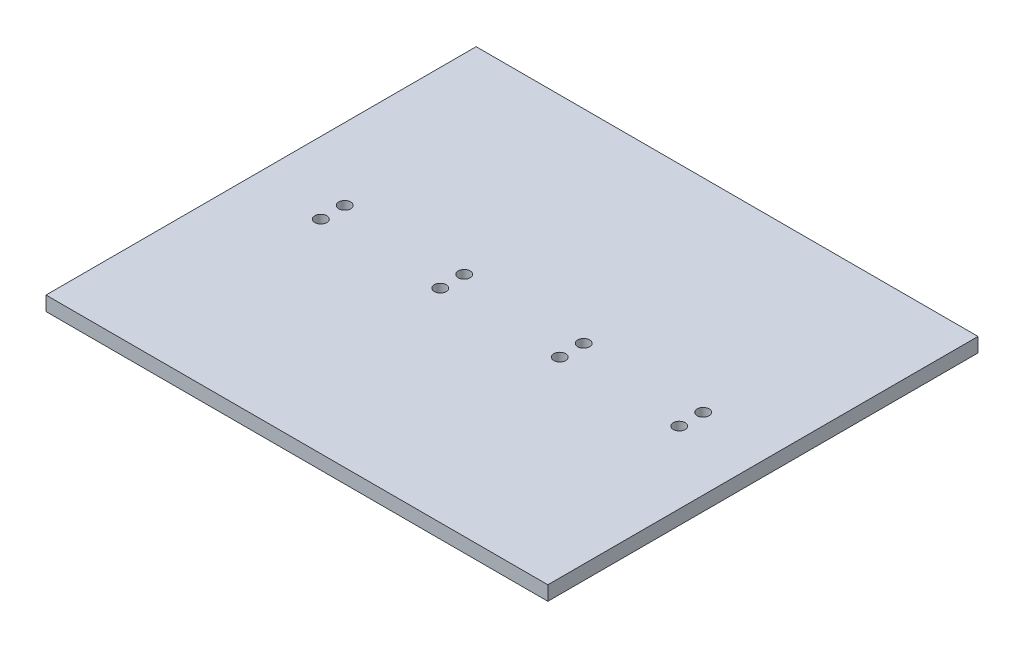
SolidWorks part; units mm, degrees
material "A-Стеклянное волокно"
ref_plane "Спереди" through (0, 0, 0) normal (0, 0, 1) x (1, 0, 0)
ref_plane "Сверху" through (0, 0, 0) normal (0, 1, 0) x (1, 0, 0)
ref_plane "Справа" through (0, 0, 0) normal (1, 0, 0) x (0, 0, -1)
sketch "Эскиз1" plane through (0, 0, 0) normal (0, 1, 0) x (1, 0, 0)
  line L1 (-5.25, -4.5) -> (5.25, -4.5)
  line L2 (-5.25, -4.5) -> (-5.25, 4.5)
  line L3 (-5.25, 4.5) -> (5.25, 4.5)
  line L4 (5.25, -4.5) -> (5.25, 4.5)
  line L5 (-5.25, -4.5) -> (5.25, 4.5) construction
  line L6 (-5.25, 4.5) -> (5.25, -4.5) construction
  point P0 (0, 0)
  dimension "D1" = 10.5
  dimension "D2" = 9
extrude "Бобышка-Вытянуть1" add sketch "Эскиз1" along normal blind 0.3
sketch "Эскиз2" plane through (0, 0.3, 0) normal (0, 1, 0) x (1, 0, 0)
  circle A0 centre (-3.75, 0.25) radius 0.125
  circle A1 centre (-1.25, 0.25) radius 0.125
  circle A2 centre (1.25, 0.25) radius 0.125
  circle A3 centre (3.75, 0.25) radius 0.125
  circle A4 centre (-1.25, -0.25) radius 0.125
  circle A5 centre (1.25, -0.25) radius 0.125
  circle A6 centre (3.75, -0.25) radius 0.125
  circle A7 centre (-3.75, -0.25) radius 0.125
  dimension "D1" = 0.25
  dimension "D2" = 0.25
  dimension "D3" = 3.75
  dimension "D4" = 4
  dimension "D5" = 2
extrude "Вырез-Вытянуть1" cut sketch "Эскиз2" against normal through all
